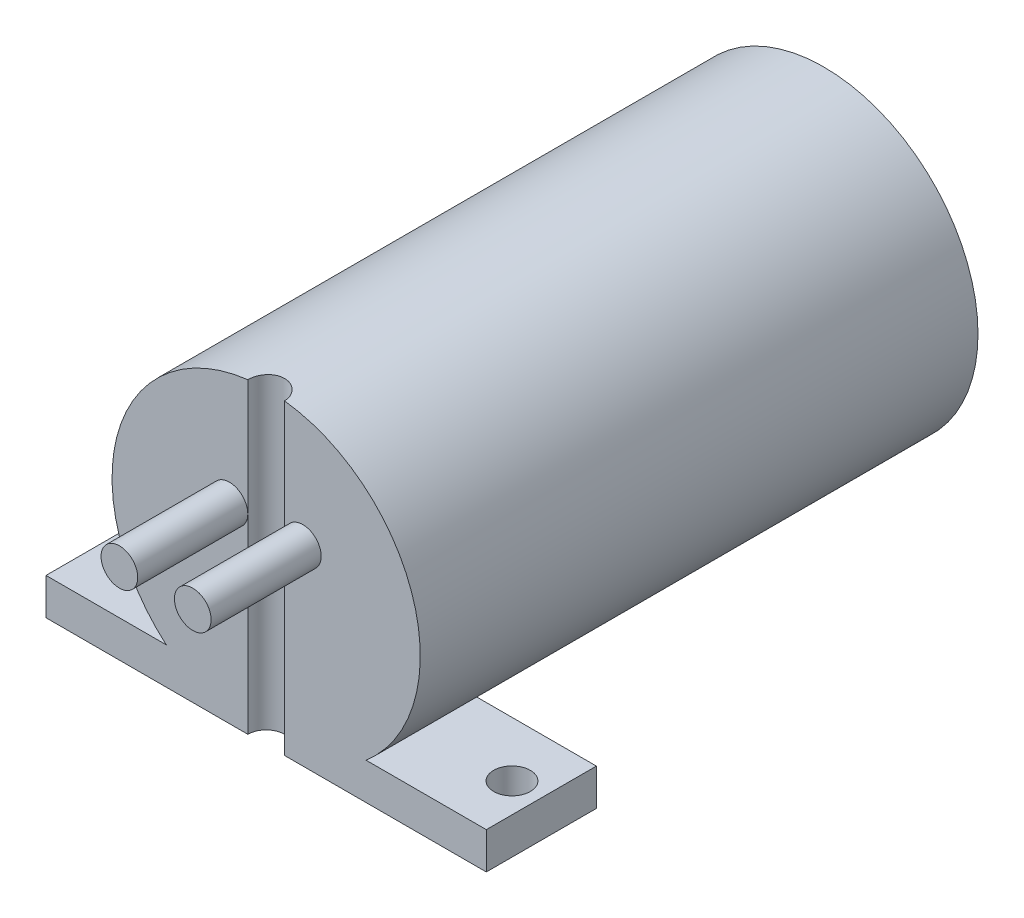
SolidWorks part; units mm, degrees
ref_plane "Front Plane" through (0, 0, 0) normal (0, 0, 1) x (1, 0, 0)
ref_plane "Top Plane" through (0, 0, 0) normal (0, 1, 0) x (1, 0, 0)
ref_plane "Right Plane" through (0, 0, 0) normal (1, 0, 0) x (0, 0, -1)
sketch "Sketch1" plane through (0, 0, 0) normal (0, 0, 1) x (1, 0, 0)
  circle A0 centre (0, 0) radius 13.335
  dimension "D1" = 26.67
extrude "Boss-Extrude1" add sketch "Sketch1" along normal blind 48.26
ref_plane "Plane1" through (0, -13.335, 0) normal (0, -1, 0) x (-1, 0, 0)
sketch "Sketch2" plane through (0, -13.335, 0) normal (0, -1, 0) x (-1, 0, 0)
  line L0 (-13.335, -48.26) -> (13.335, -48.26) construction
  line L1 (-19.05, -38.735) -> (19.05, -38.735)
  line L2 (-19.05, -38.735) -> (-19.05, -48.26)
  line L3 (-19.05, -48.26) -> (19.05, -48.26)
  line L4 (19.05, -38.735) -> (19.05, -48.26)
  point P4 (0, -48.26)
  dimension "D1" = 38.1
  dimension "D2" = 9.525
extrude "Boss-Extrude2" add sketch "Sketch2" against normal blind 3.175
sketch "Sketch3" plane through (0, -13.335, 0) normal (0, -1, 0) x (-1, 0, 0)
  line L0 (-19.05, -48.26) -> (19.05, -48.26) construction
  point P0 (-16.51, -43.4975)
  point P1 (16.51, -43.4975)
  point P2 (0, 0)
  point P4 (0, -48.26)
  dimension "D1" = 33.02
  dimension "D2" = 16.51
  dimension "D3" = 4.7625
hole_wizard "1/8 (0.125) Diameter Hole1" positions "Sketch3" profile "Sketch4" hole size "1/8" standard "ANSI Inch" end condition through all
sketch "Sketch4" plane through (16.51, -13.335, 43.4975) normal (1, 0, 0) x (0, 0, -1)
  line L0 (0, 0) -> (0, 26.67)
  line L1 (0, 26.67) -> (1.5875, 26.67)
  line L2 (1.5875, 26.67) -> (1.5875, 0)
  line L5 (1.5875, 0) -> (0, 0)
  line L11 (0, -6.35) -> (0, 107.95) construction
  dimension "Thru Hole Dia." = 3.175
  dimension "Thru Hole Depth" = 26.67
sketch "Sketch5" plane through (0, 0, 48.26) normal (0, 0, 1) x (1, 0, 0)
  circle A0 centre (-3.175, 3.175) radius 1.5875
  circle A1 centre (3.175, 3.175) radius 1.5875
  point P4 (4.3544, 4.7644)
  point P5 (0, 0)
  point P7 (3.175, 2.9267)
  dimension "D1" = 3.175
  dimension "D2" = 3.175
  dimension "D3" = 3.175
  dimension "D4" = 3.175
  dimension "D5" = 3.175
extrude "Boss-Extrude3" add sketch "Sketch5" along normal blind 9.525
